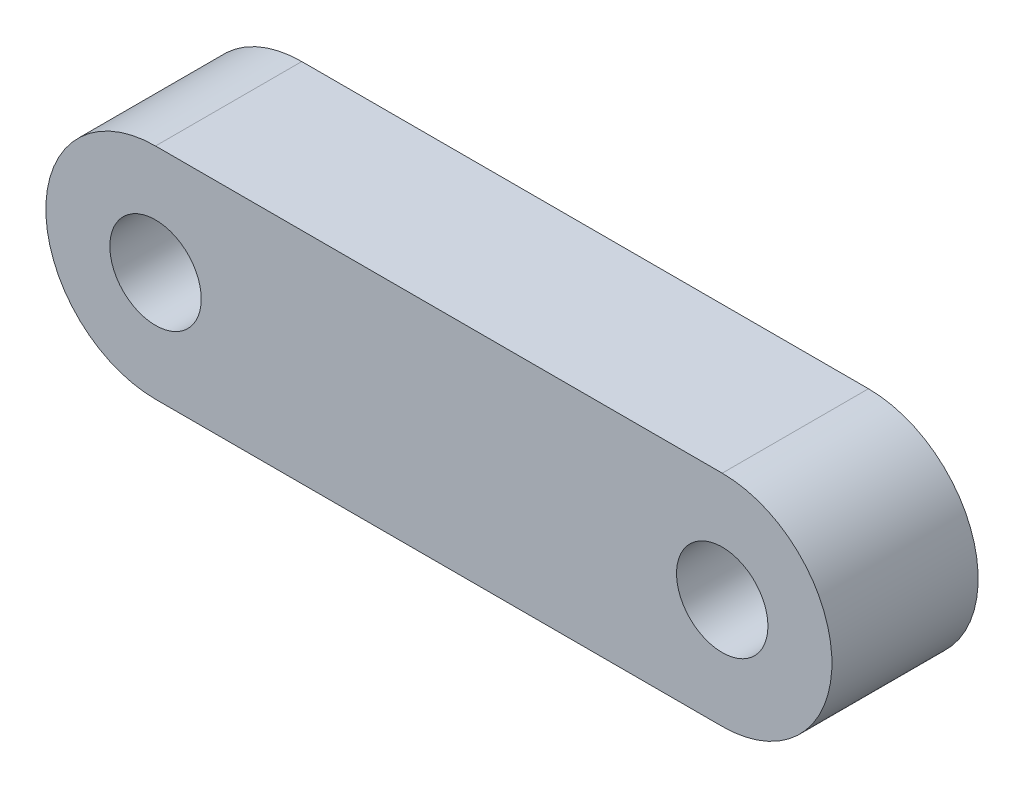
SolidWorks part; units mm, degrees
ref_plane "Plano frontal" through (0, 0, 0) normal (0, 0, 1) x (1, 0, 0)
ref_plane "Plano superior" through (0, 0, 0) normal (0, 1, 0) x (1, 0, 0)
ref_plane "Plano direito" through (0, 0, 0) normal (1, 0, 0) x (0, 0, -1)
sketch "Esboço1" plane through (0, 0, 0) normal (0, 0, 1) x (1, 0, 0)
  line L0 (-7.75, 0) -> (7.75, 0) construction
  line L1 (-7.75, 3) -> (7.75, 3)
  line L2 (-7.75, -3) -> (7.75, -3)
  arc A0 (-7.75, 3) -> (-7.75, -3) centre (-7.75, 0) ccw
  arc A1 (7.75, -3) -> (7.75, 3) centre (7.75, 0) ccw
  point P3 (0, 0)
  dimension "D1" = 3
  dimension "D2" = 15.5
extrude "Ressalto-extrusão1" add sketch "Esboço1" along normal blind 4
hole_wizard "Furo roscado de M3x0.51" positions "Esboço3" profile "Esboço4" tap size "M3x0.5" standard "Ansi Metric" end condition through all
sketch "Esboço3" plane through (0, 0, 4) normal (0, 0, 1) x (1, 0, 0)
  point P0 (7.75, 0)
  point P3 (-7.75, 0)
sketch "Esboço4" plane through (7.75, 0, 4) normal (1, 0, 0) x (0, -1, 0)
  line L0 (0, 0) -> (0, 4)
  line L1 (0, 4) -> (1.25, 4)
  line L2 (1.25, 4) -> (1.25, 0)
  line L5 (1.25, 0) -> (0, 0)
  line L11 (0, -6.35) -> (0, 107.95) construction
  dimension "Thread Major Dia." = 2.5
  dimension "Thru Tap Drill Depth" = 4
